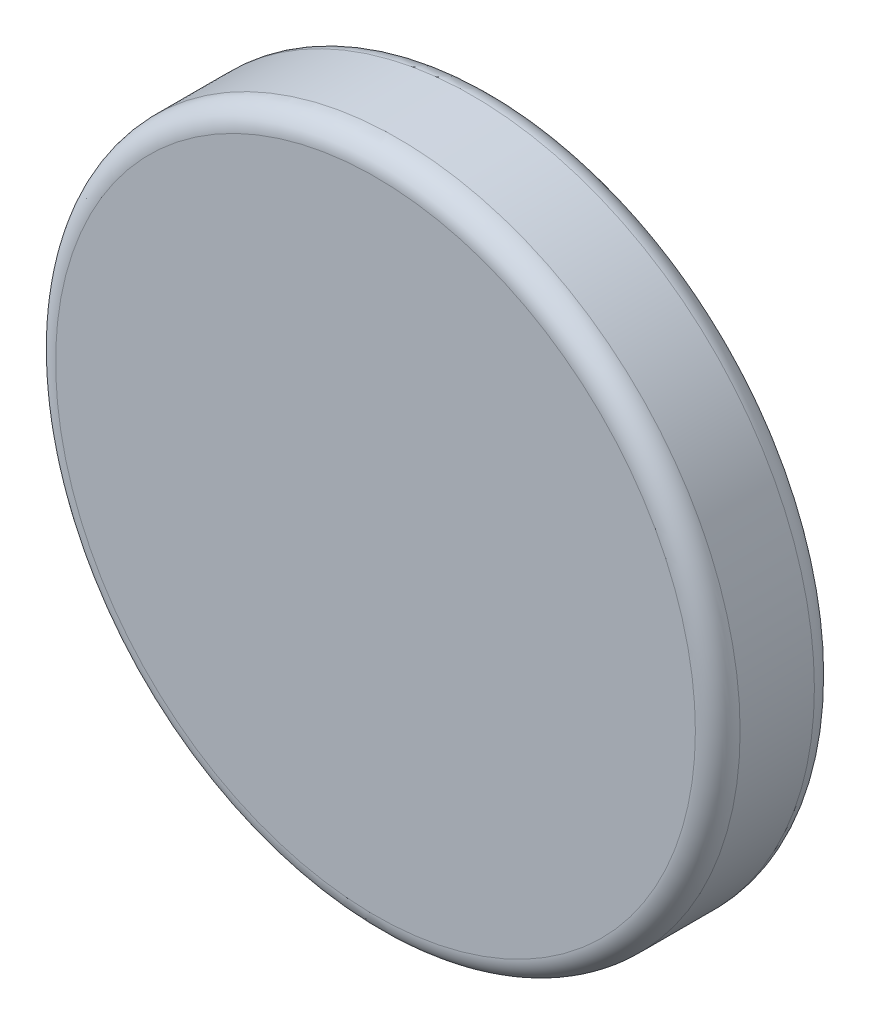
SolidWorks part; units mm, degrees
ref_plane "Přední rovina" through (0, 0, 0) normal (0, 0, 1) x (1, 0, 0)
ref_plane "Horní rovina" through (0, 0, 0) normal (0, 1, 0) x (1, 0, 0)
ref_plane "Pravá rovina" through (0, 0, 0) normal (1, 0, 0) x (0, 0, -1)
sketch "Skica1" plane through (0, 0, 0) normal (0, 0, 1) x (1, 0, 0)
  circle A0 centre (0, 0) radius 76.5
  dimension "D1" = 153
extrude "Přidat vysunutím1" add sketch "Skica1" along normal blind 20 and the other way blind 6.6
sketch "Skica2" plane through (0, 0, -6.6) normal (0, 0, -1) x (-1, 0, 0)
  line L0 (25, -10) -> (48.8, -10)
  line L1 (-10, 48.8) -> (10, 48.8)
  line L2 (10, 48.8) -> (10, 25)
  line L3 (10, 25) -> (25, 25)
  line L4 (25, 25) -> (25, 10)
  line L5 (25, 10) -> (48.8, 10)
  line L6 (48.8, 10) -> (48.8, -10)
  line L7 (0, 83.4805) -> (0, -84.3899) construction
  line L8 (-83.8391, 0) -> (96.8364, 0) construction
  line L9 (25, -25) -> (25, -10)
  line L10 (10, -25) -> (25, -25)
  line L11 (10, -48.8) -> (10, -25)
  line L12 (-10, -48.8) -> (10, -48.8)
  line L13 (-10, -48.8) -> (-10, -25)
  line L14 (-10, -25) -> (-25, -25)
  line L15 (-25, -25) -> (-25, -10)
  line L16 (-48.8, 10) -> (-48.8, -10)
  line L17 (-25, 10) -> (-48.8, 10)
  line L18 (-25, 25) -> (-25, 10)
  line L19 (-10, 25) -> (-25, 25)
  line L20 (-10, 48.8) -> (-10, 25)
  line L21 (-25, -10) -> (-48.8, -10)
  point P0 (0, 0)
  point P1 (-17.5, -25)
  point P12 (0, 0)
  point P13 (17.5, 25)
  point P15 (48.8, 0)
  point P18 (17.5, -25)
  point P23 (0, -48.8)
  point P32 (0, 48.8)
  point P33 (-48.8, 0)
  dimension "D1" = 48.8
  dimension "D2" = 48.8
  dimension "D3" = 25
  dimension "D4" = 25
  dimension "D5" = 10
  dimension "D6" = 20
extrude "Odebrat vysunutím1" cut sketch "Skica2" against normal blind 5
fillet "Zaoblit1" radius 2 20 edges at (-36.9, -10, -6.6) (-25, -17.5, -6.6) (-17.5, -25, -6.6) (-10, -36.9, -6.6) (0, -48.8, -6.6) (17.5, -25, -6.6) (36.9, -10, -6.6) (10, -36.9, -6.6) (25, -17.5, -6.6) (48.8, 0, -6.6) (36.9, 10, -6.6) (-48.8, 0, -6.6) (-36.9, 10, -6.6) (-25, 17.5, -6.6) (-17.5, 25, -6.6) (-10, 36.9, -6.6) (0, 48.8, -6.6) (10, 36.9, -6.6) (17.5, 25, -6.6) (25, 17.5, -6.6)
fillet "Zaoblit2" radius 5 2 edges at (76.5, 0, 20) (76.5, 0, -6.6)
